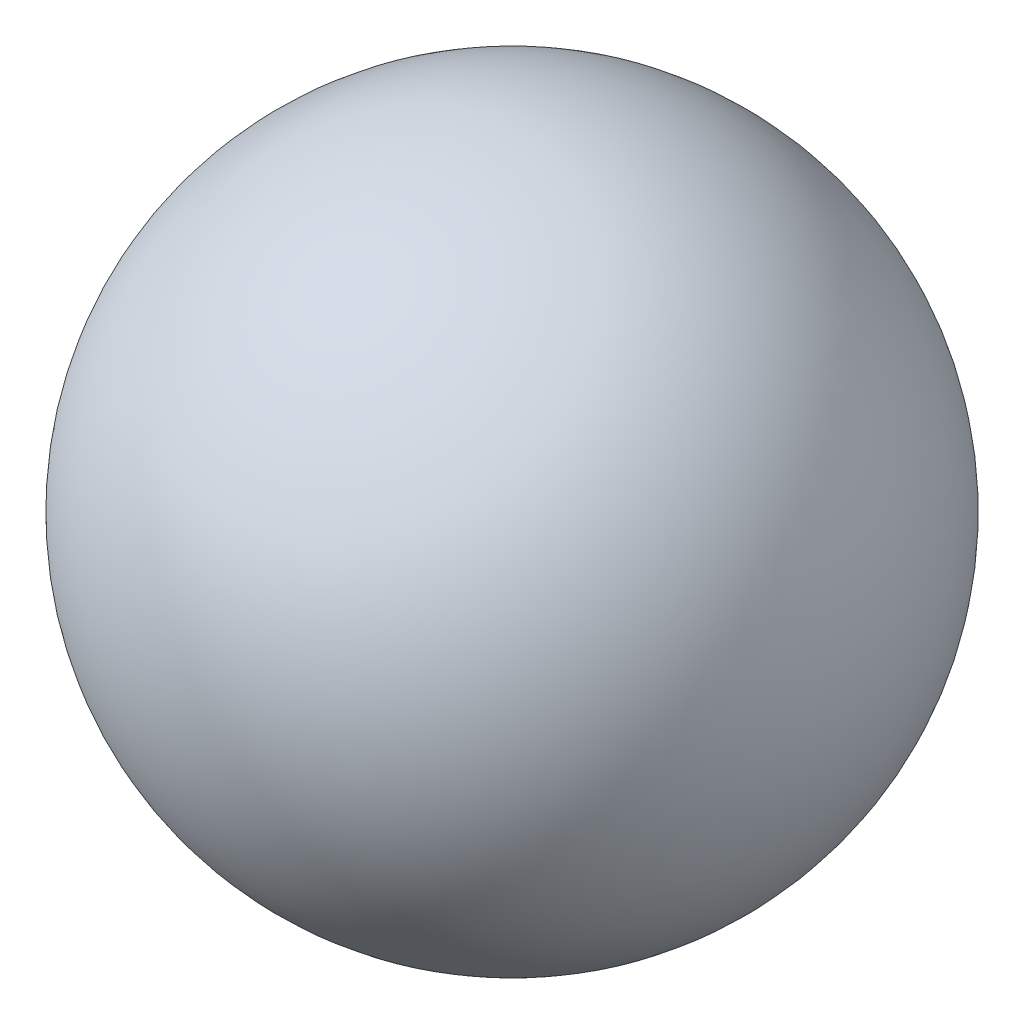
SolidWorks part; units mm, degrees
ref_plane "Front Plane" through (0, 0, 0) normal (0, 0, 1) x (1, 0, 0)
ref_plane "Top Plane" through (0, 0, 0) normal (0, 1, 0) x (1, 0, 0)
ref_plane "Right Plane" through (0, 0, 0) normal (1, 0, 0) x (0, 0, -1)
sketch "Sketch1" plane through (0, 0, 0) normal (0, 0, 1) x (1, 0, 0)
  line L0 (0, 0) -> (0, 62.3224) construction
  line L1 (0, 40.8781) -> (0, -62.3224) construction
  line L2 (0, 62.3224) -> (0, -62.3224)
  arc A0 (0, -62.3224) -> (0, 62.3224) centre (0, 0) cw
revolve "Revolve1" add sketch "Sketch1" angle 360 about L2
